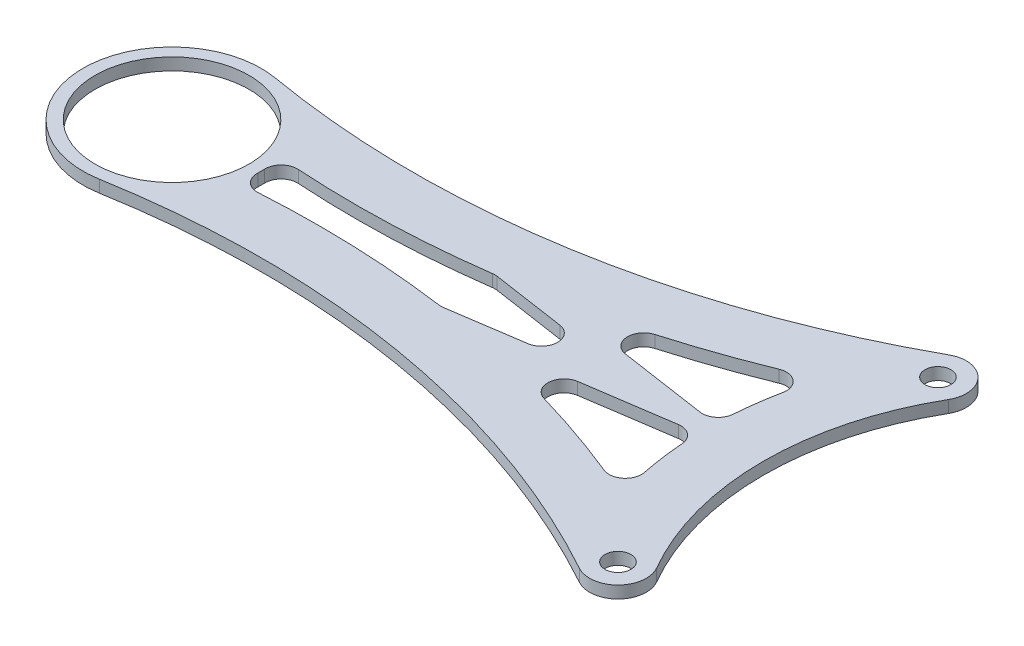
SolidWorks part; units mm, degrees
material "Thornel Mat VMA"
ref_plane "Front Plane" through (0, 0, 0) normal (0, 0, 1) x (1, 0, 0)
ref_plane "Top Plane" through (0, 0, 0) normal (0, 1, 0) x (1, 0, 0)
ref_plane "Right Plane" through (0, 0, 0) normal (1, 0, 0) x (0, 0, -1)
sketch "Sketch1" plane through (0, 0, 0) normal (0, 1, 0) x (1, 0, 0)
  line L0 (0, 0) -> (-43, 0) construction
  line L1 (0, 0) -> (-37.2391, 21.5) construction
  line L2 (0, 0) -> (-37.2391, -21.5) construction
  arc A0 (-37.2391, 21.5) -> (-37.2391, -21.5) centre (0, 0) ccw
  arc A1 (-107.1267, 10.8393) -> (-107.1267, -10.8393) centre (-109, 0) ccw
  arc A2 (-31.1769, 18) -> (-31.1769, -18) centre (0, 0) ccw
  circle A3 centre (-34.208, 19.75) radius 3.5
  circle A4 centre (-34.208, -19.75) radius 3.5
  arc A5 (-107.1267, 10.8393) -> (-35.8991, 22.8144) centre (-88.564, 118.2471) ccw
  arc A6 (-107.1267, -10.8393) -> (-35.8991, -22.8144) centre (-88.564, -118.2471) cw
  dimension "D2" = 22
  dimension "D3" = 86
  dimension "D4" = 7
  dimension "D7" = 109
  dimension "D1" = 109
  dimension "D5" = 30
  dimension "D6" = 30
  dimension "D8" = 0
extrude "Boss-Extrude1" add sketch "Sketch1" along normal mid plane 1.5 contours A1 A6 A4 A0 A3 A5 | A4 A2 A3 A0 | A4 | A3
hole_wizard "Ø3.2 (3.2) Diameter Hole1" positions "Sketch5" profile "Sketch4" hole size "Ø3.2" standard "ANSI Metric"
sketch "Sketch5" plane through (0, 0.75, 0) normal (0, 1, 0) x (1, 0, 0)
  circle A0 centre (-109, 0) radius 11
  circle A1 centre (-106.5307, 14.2882) radius 3.5
  circle A2 centre (-106.5307, -14.2882) radius 3.5
  arc A3 (-35.8991, -22.8144) -> (-107.1267, -10.8393) centre (-88.564, -118.2471) ccw construction
  arc A4 (-107.1267, 10.8393) -> (-35.8991, 22.8144) centre (-88.564, 118.2471) ccw construction
  point P0 (-34.208, 19.75)
  point P3 (-34.208, -19.75)
  point P11 (-106.5307, 14.2882)
  point P13 (-106.5307, -14.2882)
  dimension "D1" = 7
sketch "Sketch4" plane through (-34.208, 0.75, -19.75) normal (1, 0, 0) x (0, 0, 1)
  line L0 (0, 0) -> (0, 10.9614)
  line L1 (0, 10.9614) -> (1.6, 10)
  line L2 (1.6, 10) -> (1.6, 0)
  line L5 (1.6, 0) -> (0, 0)
  line L10 (0, 10.9614) -> (-1.6, 10) construction
  line L11 (0, -6.35) -> (0, 107.95) construction
  dimension "Hole Dia." = 3.2
  dimension "Hole Depth" = 10
  dimension "Drill Angle" = 118
sketch "Sketch6" plane through (0, 0.75, 0) normal (0, 1, 0) x (1, 0, 0)
  line L0 (-43, 0) -> (-69.1391, -3.8851)
  line L1 (-43, 0) -> (-69.1391, 3.8851)
  line L2 (-42.853, 0.9891) -> (-68.9921, 4.8742)
  line L3 (-43.147, -0.9891) -> (-72.4693, 3.369)
  line L4 (-43.147, 0.9891) -> (-72.4693, -3.369)
  line L5 (-42.853, -0.9891) -> (-68.9921, -4.8742)
  line L6 (-43.147, -0.9891) -> (-69.2861, 2.8959) construction
  line L7 (-43.147, 0.9891) -> (-69.2861, -2.8959) construction
  arc A2 (-108.3188, 3.9416) -> (-32.5169, 16.6856) centre (-88.564, 118.2471) ccw
  arc A3 (-98.3261, 2.6586) -> (-41.184, 12.3644) centre (-88.564, 118.2471) ccw
  arc A5 (-32.5169, -16.6856) -> (-108.3188, -3.9416) centre (-88.564, -118.2471) ccw
  arc A6 (-41.184, -12.3644) -> (-98.3261, -2.6586) centre (-88.564, -118.2471) ccw
  arc A7 (-98.3261, -2.6586) -> (-98.3261, 2.6586) centre (-109, 0) ccw
  arc A8 (-37.2391, 21.5) -> (-37.2391, -21.5) centre (0, 0) ccw
  arc A9 (-41.184, 12.3644) -> (-41.184, -12.3644) centre (0, 0) ccw
  dimension "D1" = 7
  dimension "D2" = 7
  dimension "D3" = 7
  dimension "D4" = 1
  dimension "D5" = 1
  dimension "D6" = 1
  dimension "D7" = 1
extrude "Cut-Extrude1" cut sketch "Sketch6" against normal through all contours A7 A6 L4 L3 A3 | A9 A3 L2 | A9 L5 A6
fillet "Fillet1" radius 2 11 edges at (-41.184, 0, 12.3644) (-42.9882, 0, -1.0092) (-41.184, 0, -12.3644) (-42.9882, 0, 1.0092) (-66.0961, 0, -4.4438) (-66.0961, 0, 4.4438) (-49.802, 0, 0) (-72.4693, 0, 3.369) (-72.4693, 0, -3.369) (-98.3261, 0, 2.6586) (-98.3261, 0, -2.6586)
sketch "Sketch7" plane through (0, 0.75, 0) normal (0, 1, 0) x (1, 0, 0)
  circle A0 centre (-109, 0) radius 9.5
  dimension "D1" = 19
extrude "Cut-Extrude2" cut sketch "Sketch7" against normal through all
